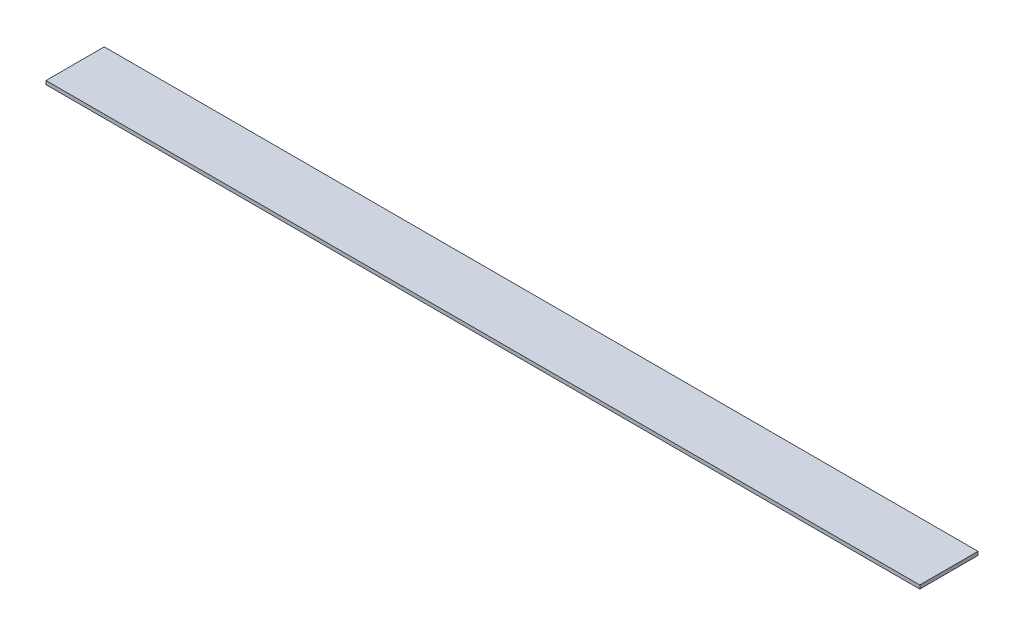
SolidWorks part; units mm, degrees
ref_plane "Front Plane" through (0, 0, 0) normal (0, 0, 1) x (1, 0, 0)
ref_plane "Top Plane" through (0, 0, 0) normal (0, 1, 0) x (1, 0, 0)
ref_plane "Right Plane" through (0, 0, 0) normal (1, 0, 0) x (0, 0, -1)
sketch "Sketch1" plane through (0, 0, 0) normal (0, 1, 0) x (1, 0, 0)
  line L1 (0, 0) -> (381, 0)
  line L2 (0, 0) -> (0, 25.4)
  line L3 (0, 25.4) -> (381, 25.4)
  line L4 (381, 0) -> (381, 25.4)
  dimension "D1" = 25.4
  dimension "D2" = 381
extrude "Boss-Extrude1" add sketch "Sketch1" along normal blind 1.5875
